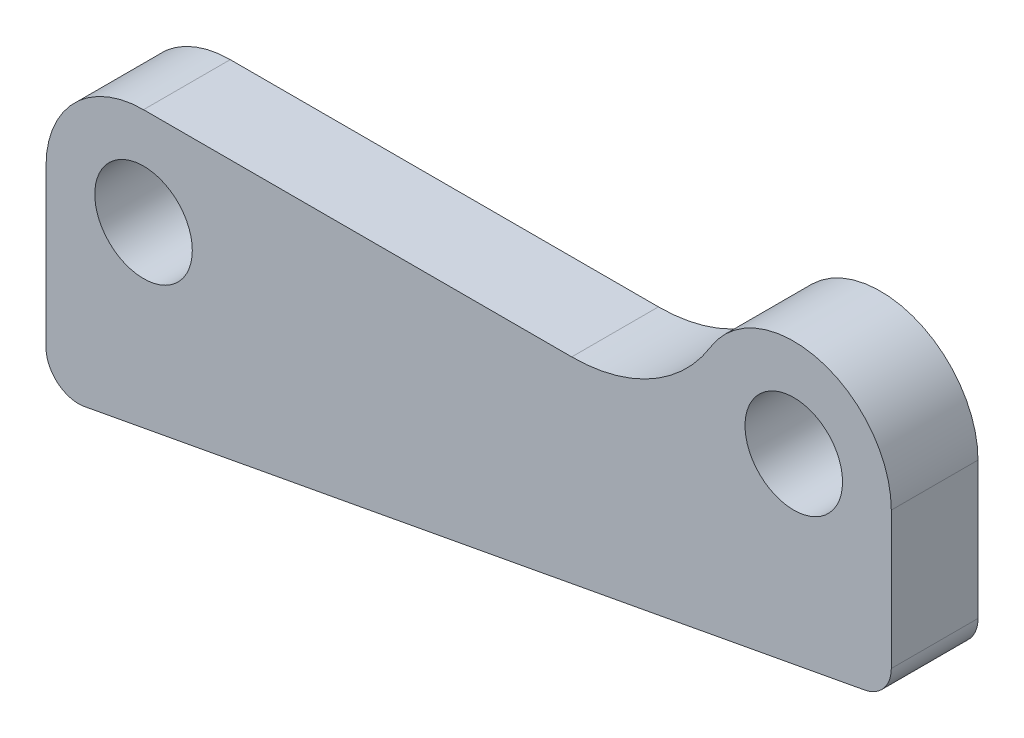
SolidWorks part; units mm, degrees
ref_plane "Plane1" through (0, 0, 0) normal (0, 0, 1) x (1, 0, 0)
ref_plane "Plane2" through (0, 0, 0) normal (0, 1, 0) x (1, 0, 0)
ref_plane "Plane3" through (0, 0, 0) normal (1, 0, 0) x (0, 0, -1)
sketch "Sketch1" plane through (0, 0, 0) normal (0, 0, 1) x (1, 0, 0)
  line L0 (-9, 0) -> (-9, -14.5)
  line L1 (-5.4533, -17.4498) -> (66.5467, -4.1054)
  line L2 (69, -1.1556) -> (69, 11.5)
  line L3 (39.5122, 9) -> (0, 9)
  circle A0 centre (0, 0) radius 4.5
  circle A1 centre (60, 11.5) radius 4.5
  arc A2 (0, 9) -> (-9, 0) centre (0, 0) ccw
  arc A3 (-9, -14.5) -> (-5.4533, -17.4498) centre (-6, -14.5) ccw
  arc A4 (66.5467, -4.1054) -> (69, -1.1556) centre (66, -1.1556) ccw
  arc A5 (69, 11.5) -> (52.3171, 16.1875) centre (60, 11.5) ccw
  arc A6 (52.3171, 16.1875) -> (39.5122, 9) centre (39.5122, 24) cw
  dimension "D1" = 9
  dimension "D3" = 9
  dimension "D5" = 3
  dimension "D7" = 26.5
  dimension "D8" = 15
  dimension "D4" = 9
  dimension "D2" = 60
  dimension "D6" = 79.5
  dimension "D9" = 11.5
  dimension "D10" = 16.5371
  dimension "D11" = 16.1638
extrude "Extrude1" add sketch "Sketch1" along normal blind 8
